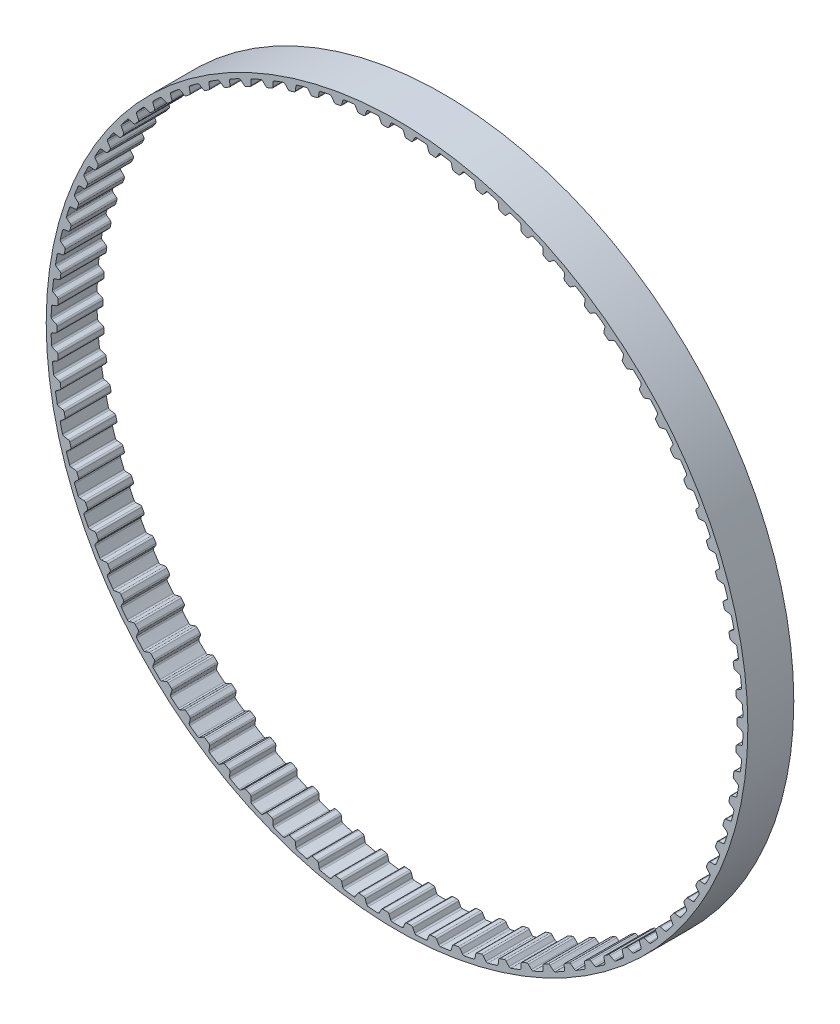
SolidWorks part; units mm, degrees
ref_plane "Front Plane" through (0, 0, 0) normal (0, 0, 1) x (1, 0, 0)
ref_plane "Top Plane" through (0, 0, 0) normal (0, 1, 0) x (1, 0, 0)
ref_plane "Right Plane" through (0, 0, 0) normal (1, 0, 0) x (0, 0, -1)
sketch "Sketch1" plane through (0, 0, 0) normal (0, 0, 1) x (1, 0, 0)
  line L0 (0, 0) -> (-2.4597, 70.4368) construction
  line L1 (0, 0) -> (2.4597, 70.4368) construction
  line L2 (2.4597, 70.4368) -> (-2.4597, 70.4368) construction
  line L3 (2.4597, 70.4368) -> (-2.4597, 70.4368) construction
  circle A0 centre (0, 0) radius 72.7657
  circle A1 centre (0, 0) radius 70.4797
  circle A2 centre (0, 0) radius 71.7497 construction
  dimension "OD" = 145.5314
  dimension "Angle Distance" = 4
  dimension "hs" = 2.286
  dimension "ht" = 1.27
extrude "Boss-Extrude1" add sketch "Sketch1" along normal mid plane 9.525
sketch "Sketch2" plane through (0, 0, 0) normal (0, 0, 1) x (1, 0, 0)
  line L1 (0, 72.7657) -> (0, 0) construction
  line L2 (-2.54, 71.1002) -> (2.54, 71.1002) construction
  line L4 (-1.7635, 70.4611) -> (-3.1559, 70.4125)
  line L5 (-1.7635, 70.4611) -> (-1.2209, 71.7393)
  line L6 (-3.1559, 70.4125) -> (-3.7863, 71.6497)
  line L7 (0, 0) -> (-2.4597, 70.4368) construction
  line L8 (-1.2209, 71.7393) -> (-3.7863, 71.6497) construction
  line L9 (1.2209, 71.7393) -> (3.7863, 71.6497) construction
  line L10 (3.1559, 70.4125) -> (3.7863, 71.6497)
  line L11 (1.7635, 70.4611) -> (1.2209, 71.7393)
  line L12 (1.7635, 70.4611) -> (3.1559, 70.4125)
  line L13 (0, 0) -> (27.8462, 67.2267) construction
  line L14 (-2.54, 71.1002) -> (-7.6071, 70.7377) construction
  line L15 (-5.0735, 70.9189) -> (0, 0) construction
  line L16 (-7.6071, 70.7377) -> (-7.5359, 70.0757) construction
  circle A0 centre (0, 0) radius 71.7497 construction
  circle A1 centre (0, 0) radius 71.7497
  circle A2 centre (0, 0) radius 71.1002 construction
  circle A4 centre (0, 0) radius 72.7657 construction
  circle A5 centre (0, 0) radius 70.4797 construction
  point P16 (-1.4922, 71.1002)
  point P20 (0, 71.1002)
  dimension "D1" = 22.5
  dimension "bt" = 2.5654
  dimension "b" = 50
  dimension "Pitch" = 5.08
sketch "Sketch3" plane through (0, 0, 0) normal (0, 0, 1) x (1, 0, 0)
  line L0 (-2.0091, 70.4511) -> (2.0091, 70.4511)
  line L2 (-1.7635, 70.4611) -> (-1.2209, 71.7393) construction
  line L3 (1.7635, 70.4611) -> (1.2209, 71.7393) construction
  line L5 (-1.6693, 70.683) -> (-1.3178, 71.511)
  line L7 (1.6693, 70.683) -> (1.3178, 71.511)
  arc A0 (1.6693, 70.683) -> (2.0091, 70.4511) centre (2.02, 70.8319) ccw
  circle A1 centre (0, 0) radius 71.7497 construction
  arc A2 (0.9723, 71.7431) -> (-0.9723, 71.7431) centre (0, 0) ccw
  arc A3 (-1.6693, 70.683) -> (-2.0091, 70.4511) centre (-2.02, 70.8319) cw
  arc A4 (1.3178, 71.511) -> (0.9723, 71.7431) centre (0.9671, 71.3621) ccw
  arc A5 (-1.3178, 71.511) -> (-0.9723, 71.7431) centre (-0.9671, 71.3621) cw
  circle A6 centre (0, 0) radius 70.4797 construction
  arc A7 (-2.0091, 70.4511) -> (2.0091, 70.4511) centre (0, 0) ccw construction
  dimension "ra" = 0.381
  dimension "rr" = 0.381
extrude "Cut-Extrude1" cut sketch "Sketch3" against normal mid plane 9.525
pattern_circular "CirPattern1" count 90 over 360 about axis through (0, 0, 0) along (0, 0, 1) of "Cut-Extrude1"
sketch "Sketch4" plane through (0, 0, 4.7625) normal (0, 0, 1) x (1, 0, 0)
  line L2 (0, 0) -> (0, 91.2822)
  line L3 (0, 91.2822) -> (106.7779, 91.2822)
  line L4 (106.7779, 0) -> (106.7779, 91.2822)
  line L6 (0, 0) -> (0, -79.914)
  line L7 (0, -79.914) -> (106.7779, -79.914)
  line L8 (106.7779, 0) -> (106.7779, -79.914)
extrude "Cut-Extrude2" [suppressed] cut sketch "Sketch4" against normal through all
sketch "Sketch5" plane through (0, 0, 4.7625) normal (0, 0, 1) x (1, 0, 0)
  line L0 (25.8789, -65.2375) -> (25.8789, 64.7625) construction
  line L1 (34.5082, 64.6917) -> (32.4688, 73.9958) construction
  circle A3 centre (100.3481, -0.2375) radius 14 construction
  arc A4 (-70.707, -14.0353) -> (-69.7784, -16.8327) centre (-24.4614, -0.2375) ccw construction
  spline S0 degree 3 poles (-69.2499, -28.5833) (-72.229, 8.602) (-24.788, 90.158) (105.1598, -21.3726) (91.3918, 47.0618) (117.3469, 4.4367) (114.2093, -31.9673) (46.7298, -56.0104) (25.9793, -55.502) (6.5708, -54.7975) (-37.2287, -54.255) (-69.2499, -28.5833) (-72.229, 8.602) (-24.788, 90.158) knots -0.08893 -0.033175 -0.003318 0 0.070116 0.205226 0.601748 0.723484 0.843575 0.904908 0.908136 0.91107 0.966825 0.996682 1 1.070116 1.205226 1.601748 only from (-70.264, -15.4411) to (-70.264, -15.4411)
extrude "Extrude-Thin4" [suppressed] add sketch "Sketch5" along normal blind 20.32 thin
equation "\"D1@Cut-Extrude1\" = \"Width@Boss-Extrude1\""
